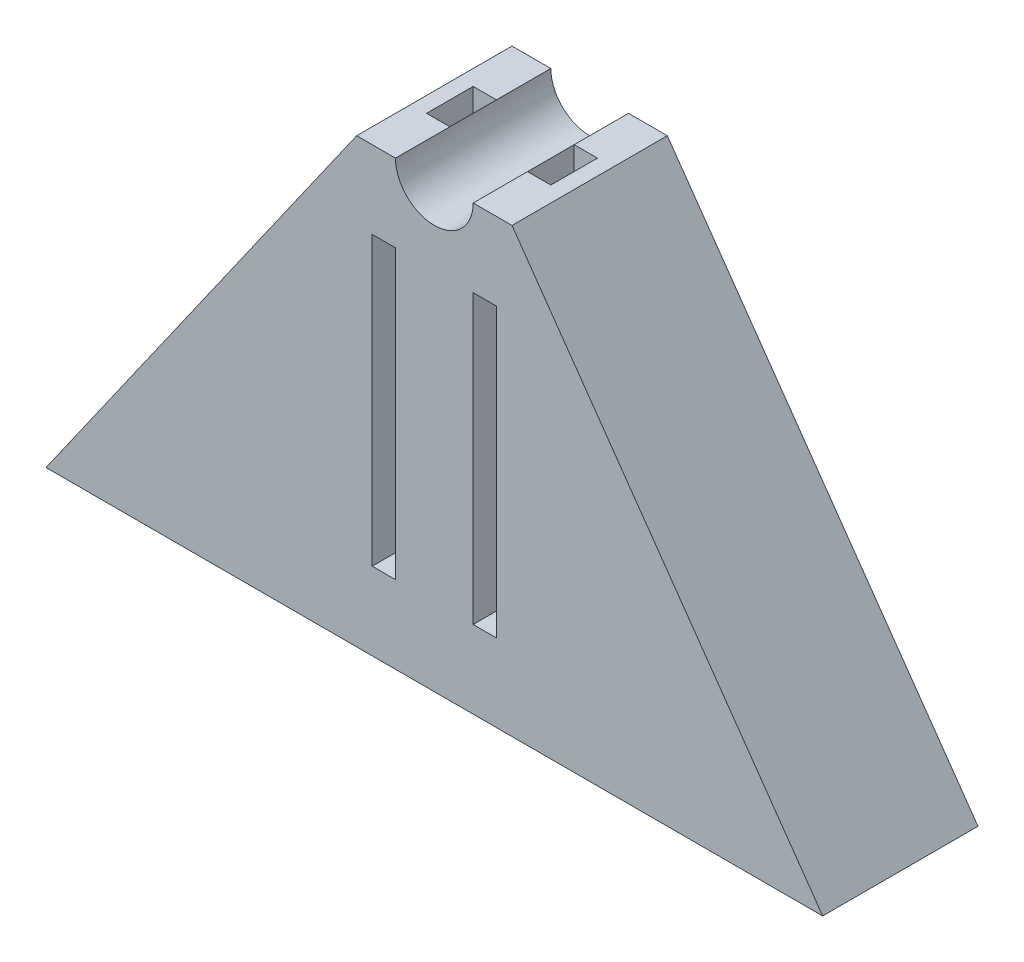
SolidWorks part; units mm, degrees
ref_plane "Front Plane" through (0, 0, 0) normal (0, 0, 1) x (1, 0, 0)
ref_plane "Top Plane" through (0, 0, 0) normal (0, 1, 0) x (1, 0, 0)
ref_plane "Right Plane" through (0, 0, 0) normal (1, 0, 0) x (0, 0, -1)
sketch "Sketch1" plane through (0, 0, 0) normal (0, 0, 1) x (1, 0, 0)
  line L0 (-25, -28.5) -> (25, -28.5)
  line L1 (25, -28.5) -> (5, 0)
  line L2 (5, 0) -> (2.5, 0)
  line L3 (-5, 0) -> (-25, -28.5)
  line L4 (0, -28.5) -> (0, 0) construction
  line L5 (-2.5, 0) -> (-5, 0)
  arc A0 (-2.5, 0) -> (2.5, 0) centre (0, 0) ccw
  point P10 (0, 0)
  point P13 (0, -2.5)
  dimension "D1" = 5
  dimension "D2" = 26
  dimension "D3" = 50
  dimension "D4" = 5
  dimension "D5" = 5
extrude "Boss-Extrude1" add sketch "Sketch1" along normal blind 10
sketch "Sketch4" plane through (0, -28.5, 0) normal (0, -1, 0) x (1, 0, 0)
  line L0 (-2.5, 5) -> (0, 5) construction
  line L1 (-4, 6.5) -> (-2.5, 6.5)
  line L2 (-4, 6.5) -> (-4, 3.5)
  line L3 (-4, 3.5) -> (-2.5, 3.5)
  line L4 (-2.5, 6.5) -> (-2.5, 3.5)
  line L5 (0, 5) -> (0, 0) construction
  dimension "D1" = 1.5
  dimension "D2" = 3
  dimension "D3" = 5
  dimension "D4" = 2.5
extrude "Cut-Extrude2" cut sketch "Sketch4" against normal through all
mirror "Mirror1" about plane through (0, 0, 0) normal (1, 0, 0) of "Cut-Extrude2"
sketch "Sketch5" plane through (0, 0, 10) normal (0, 0, 1) x (1, 0, 0)
  line L0 (2.5, -28.5) -> (4, -28.5) construction
  line L1 (4, -28.5) -> (4, 0) construction
  line L2 (4, 0) -> (2.5, 0) construction
  line L3 (2.5, 0) -> (2.5, -28.5) construction
  line L4 (-4, -28.5) -> (-2.5, -28.5) construction
  line L5 (-2.5, -28.5) -> (-2.5, 0) construction
  line L6 (-2.5, 0) -> (-4, 0) construction
  line L7 (-4, 0) -> (-4, -28.5) construction
  line L8 (2.5, -28.5) -> (4, -28.5)
  line L9 (4, -28.5) -> (4, 0)
  line L10 (4, 0) -> (2.5, 0)
  line L11 (2.5, 0) -> (2.5, -28.5)
  line L12 (-4, -28.5) -> (-2.5, -28.5)
  line L13 (-2.5, -28.5) -> (-2.5, 0)
  line L14 (-2.5, 0) -> (-4, 0)
  line L15 (-4, 0) -> (-4, -28.5)
  line L16 (-4, -5) -> (4, -5)
  line L17 (-4, -23.5) -> (4, -23.5)
  line L18 (5, 0) -> (2.5, 0) construction
  line L19 (-25, -28.5) -> (25, -28.5) construction
  dimension "D1" = 5
  dimension "D2" = 5
extrude "Cut-Extrude3" cut sketch "Sketch5" against normal through all contours L15 L17 L13 L16 | L11 L17 L9 L16
